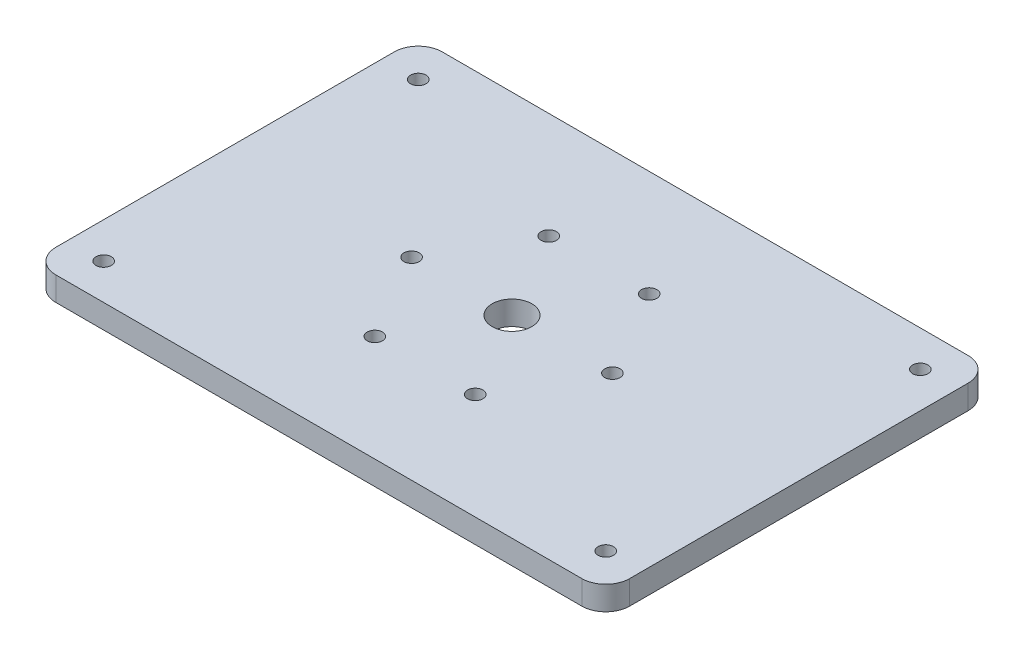
SolidWorks part; units mm, degrees
material "Acrylic (Medium-high impact)"
ref_plane "Front Plane" through (0, 0, 0) normal (0, 0, 1) x (1, 0, 0)
ref_plane "Top Plane" through (0, 0, 0) normal (0, 1, 0) x (1, 0, 0)
ref_plane "Right Plane" through (0, 0, 0) normal (1, 0, 0) x (0, 0, -1)
sketch "Sketch1" plane through (0, 0, 0) normal (0, 1, 0) x (1, 0, 0)
  line L0 (60, 80.79) -> (60, 0) construction
  line L1 (0, 0) -> (120, 0)
  line L2 (0, 0) -> (0, 80.79)
  line L3 (0, 80.79) -> (120, 80.79)
  line L4 (120, 0) -> (120, 80.79)
  line L5 (0, 40.395) -> (120, 40.395) construction
  circle A0 centre (39, 40.395) radius 1.6
  circle A1 centre (49.5, 58.5815) radius 1.6
  circle A2 centre (70.5, 58.5815) radius 1.6
  circle A3 centre (81, 40.395) radius 1.6
  circle A4 centre (60, 40.395) radius 4.15
  circle A5 centre (70.5, 22.2085) radius 1.6
  circle A6 centre (49.5, 22.2085) radius 1.6
  point P11 (60, 40.395)
  dimension "D3" = 3.2
  dimension "D4" = 21
  dimension "D6" = 8.3
  dimension "D1" = 120
  dimension "D2" = 80.79
  dimension "D5" = 6
extrude "Boss-Extrude1" add sketch "Sketch1" along normal blind 5
sketch "Sketch2" plane through (0, 5, 0) normal (0, 1, 0) x (1, 0, 0)
  line L0 (7.5, 80.79) -> (7.5, 0) construction
  line L1 (120, 80.79) -> (0, 80.79) construction
  line L2 (0, 0) -> (120, 0) construction
  line L3 (0, 40.395) -> (120, 40.395) construction
  line L4 (0, 80.79) -> (0, 0) construction
  line L5 (120, 0) -> (120, 80.79) construction
  line L6 (60, 80.79) -> (60, 0) construction
  circle A0 centre (7.5, 73.29) radius 1.6
  circle A1 centre (7.5, 7.5) radius 1.6
  circle A2 centre (112.5, 73.29) radius 1.6
  circle A3 centre (112.5, 7.5) radius 1.6
  dimension "D1" = 7.5
  dimension "D2" = 7.5
  dimension "D3" = 3.2
extrude "Cut-Extrude1" cut sketch "Sketch2" against normal through all
fillet "Fillet1" radius 5 4 edges at (120, 2.5, -80.79) (120, 2.5, 0) (0, 2.5, 0) (0, 2.5, -80.79)
